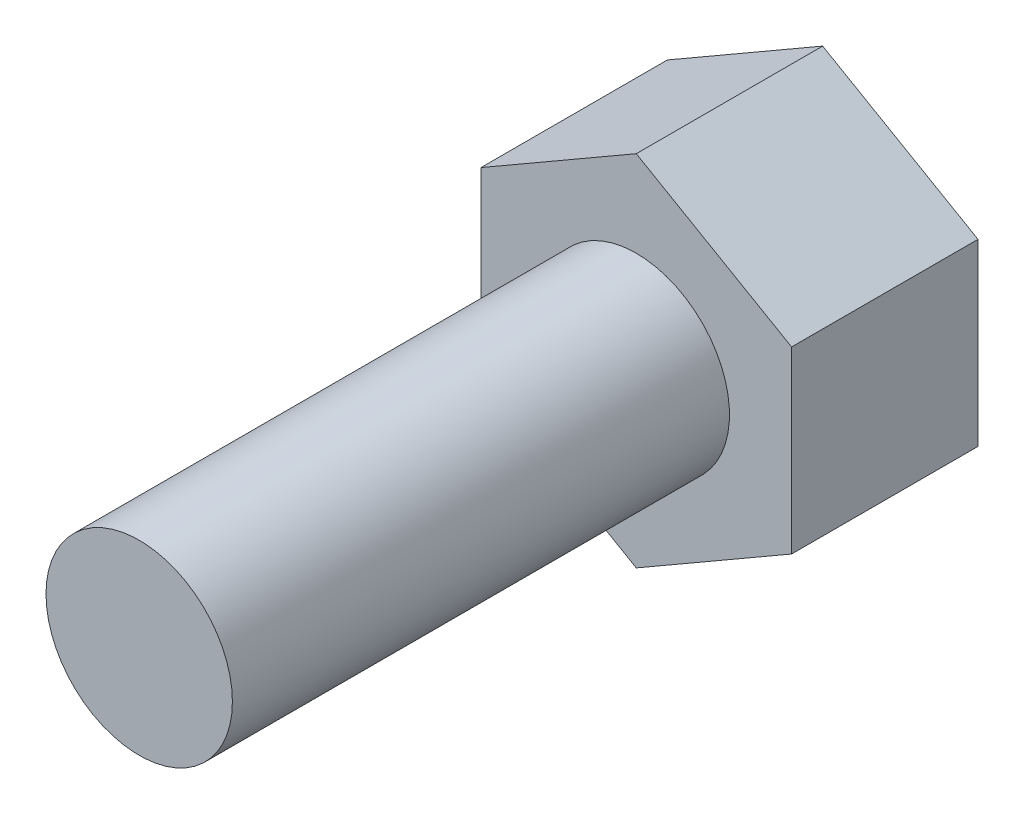
SolidWorks part; units mm, degrees
ref_plane "Front Plane" through (0, 0, 0) normal (0, 0, 1) x (1, 0, 0)
ref_plane "Top Plane" through (0, 0, 0) normal (0, 1, 0) x (1, 0, 0)
ref_plane "Right Plane" through (0, 0, 0) normal (1, 0, 0) x (0, 0, -1)
sketch "Sketch1" plane through (0, 0, 0) normal (0, 0, 1) x (1, 0, 0)
  circle A0 centre (-63.4948, 14.9787) radius 1.5
extrude "Boss-Extrude1" add sketch "Sketch1" along normal blind 8
sketch "Sketch2" plane through (0, 0, 0) normal (0, 0, -1) x (-1, 0, 0)
  line L1 (63.4948, 12.092) -> (65.9948, 13.5353)
  line L2 (65.9948, 13.5353) -> (65.9948, 16.4221)
  line L3 (65.9948, 16.4221) -> (63.4948, 17.8655)
  line L4 (63.4948, 17.8655) -> (60.9948, 16.4221)
  line L5 (60.9948, 16.4221) -> (60.9948, 13.5353)
  line L6 (60.9948, 13.5353) -> (63.4948, 12.092)
  circle A0 centre (63.4948, 14.9787) radius 2.5 construction
  dimension "D1" = 5
extrude "Boss-Extrude2" add sketch "Sketch2" along normal blind 3
